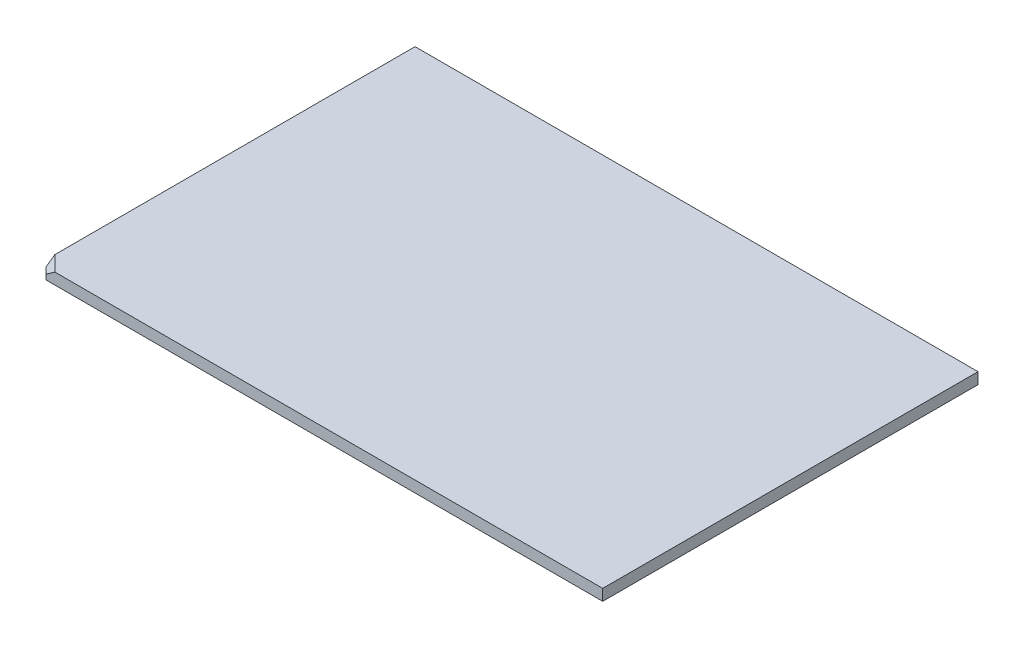
SolidWorks part; units mm, degrees
ref_plane "Front Plane" through (0, 0, 0) normal (0, 0, 1) x (1, 0, 0)
ref_plane "Top Plane" through (0, 0, 0) normal (0, 1, 0) x (1, 0, 0)
ref_plane "Right Plane" through (0, 0, 0) normal (1, 0, 0) x (0, 0, -1)
sketch "Sketch1" plane through (0, 0, 0) normal (0, 1, 0) x (1, 0, 0)
  line L1 (-26.9713, 282.5494) -> (423.0287, 282.5494)
  line L2 (-26.9713, 282.5494) -> (-26.9713, -17.4506)
  line L3 (-26.9713, -17.4506) -> (423.0287, -17.4506)
  line L4 (423.0287, 282.5494) -> (423.0287, -17.4506)
  dimension "D1" = 450
  dimension "D2" = 300
extrude "Boss-Extrude1" add sketch "Sketch1" along normal blind 9
chamfer "Chamfer1" distance 5 angle 45 1 edges at (-26.9713, 4.5, 17.4506)
chamfer "Chamfer2" distance 5 angle 45 1 edges at (-24.4713, 9, 14.9506)
